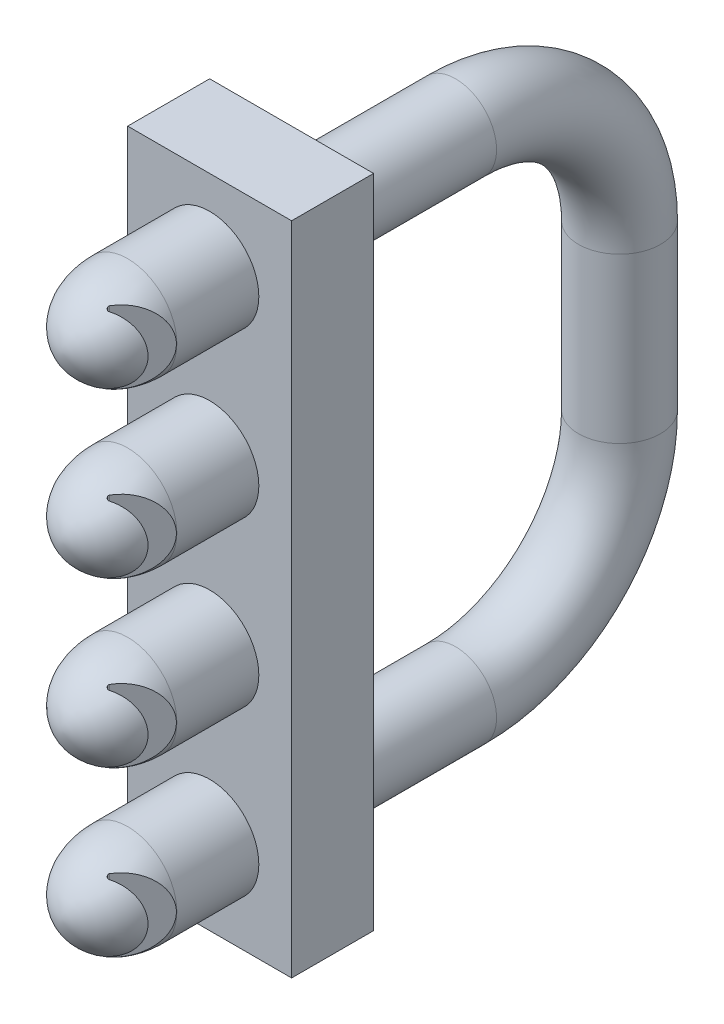
SolidWorks part; units mm, degrees
ref_plane "Front Plane" through (0, 0, 0) normal (0, 0, 1) x (1, 0, 0)
ref_plane "Top Plane" through (0, 0, 0) normal (0, 1, 0) x (1, 0, 0)
ref_plane "Right Plane" through (0, 0, 0) normal (1, 0, 0) x (0, 0, -1)
sketch "Sketch1" plane through (0, 0, 0) normal (0, 0, 1) x (1, 0, 0)
  line L1 (-5, 20) -> (5, 20)
  line L2 (-5, 20) -> (-5, -20)
  line L3 (-5, -20) -> (5, -20)
  line L4 (5, 20) -> (5, -20)
  line L5 (-5, 20) -> (5, -20) construction
  line L6 (-5, -20) -> (5, 20) construction
  point P0 (0, 0)
  dimension "D1" = 10
  dimension "D2" = 40
extrude "Boss-Extrude1" add sketch "Sketch1" along normal blind 5
ref_plane "Plane1" through (0, 0, 0) normal (1, 0, 0) x (0, 0, -1)
sketch "Sketch2" plane through (0, 0, 0) normal (0, 0, -1) x (-1, 0, 0)
  line L0 (0, 12.2341) -> (0, -12.2341) construction
  line L1 (-5, 20) -> (5, 20) construction
  circle A0 centre (0, 15) radius 2.5013
  dimension "D1" = 5.0026
  dimension "D2" = 5
sketch "Sketch3" plane through (0, 0, 0) normal (1, 0, 0) x (0, 0, -1)
  line L0 (0, 15) -> (10, 15)
  line L1 (0, 12.4987) -> (0, 17.5013) construction
  line L2 (20, 5) -> (20, -5)
  line L3 (10, -15) -> (0, -15)
  line L4 (0, -20) -> (0, 20) construction
  line L5 (-5, -20) -> (0, -20) construction
  arc A0 (20, 5) -> (10, 15) centre (10, 5) ccw
  arc A1 (10, -15) -> (20, -5) centre (10, -5) ccw
  dimension "D3" = 10
  dimension "D4" = 10
  dimension "D1" = 5
  dimension "D2" = 20
sweep "Sweep1" add profiles "Sketch2" path "Sketch3"
sketch "Sketch5" plane through (0, 0, 5) normal (0, 0, 1) x (1, 0, 0)
  line L0 (0, -12.2341) -> (0, 12.2341) construction
  line L1 (5, 20) -> (-5, 20) construction
  circle A0 centre (0, 15) radius 3
  dimension "D1" = 6
  dimension "D2" = 5
extrude "Boss-Extrude2" add sketch "Sketch5" along normal blind 5
sketch "Sketch9" plane through (0, 0, 0) normal (1, 0, 0) x (0, 0, -1)
  line L0 (-10, 15) -> (-14, 15)
  line L1 (-10, 18) -> (-10, 12) construction
  line L2 (-10, 18) -> (-10, 15)
  spline S0 degree 3 poles (-10, 18) (-13.2247, 17.9412) (-14, 15.6857) (-14, 15) knots 0 0 0 0 1 1 1 1
  dimension "D1" = 4
revolve "Revolve2" add sketch "Sketch9" angle 360 about L0
pattern_linear "LPattern2" count 4 spacing 10 along (0, -1, 0) of "Boss-Extrude2"
pattern_linear "LPattern5" count 4 spacing 10 along (0, 1, 0) of "Revolve2"
ref_plane "Plane3" through (0, 12, 0) normal (0, -1, 0) x (-1, 0, 0)
sketch "Sketch12" plane through (0, 12, 0) normal (0, -1, 0) x (-1, 0, 0)
  line L0 (0, -10) -> (0, -15.1258) construction
  line L1 (-3, -10) -> (3, -10) construction
  line L2 (0, 12.2341) -> (0, -12.2341) construction
  line L3 (0, -13.33) -> (-4.1773, -9.8249) construction
  line L4 (-0.766, -12.6872) -> (-4.5065, -10.5277)
  line L5 (-4.5065, -10.5277) -> (-3.5423, -9.3786)
  line L6 (-3.5423, -9.3786) -> (-0.766, -12.6872)
  dimension "D1" = 3.33
  dimension "D2" = 50
  dimension "D3" = 10
  dimension "D4" = 10
  dimension "D5" = 1.5
  dimension "D6" = 1
extrude "Cut-Extrude2" cut sketch "Sketch12" along normal through all and the other way through all
fillet "Fillet4" radius 0.1 4 edges at (0.766, 15, 12.6872) (0.766, 5, 12.6872) (0.766, -5, 12.6872) (0.766, -15, 12.6872)
